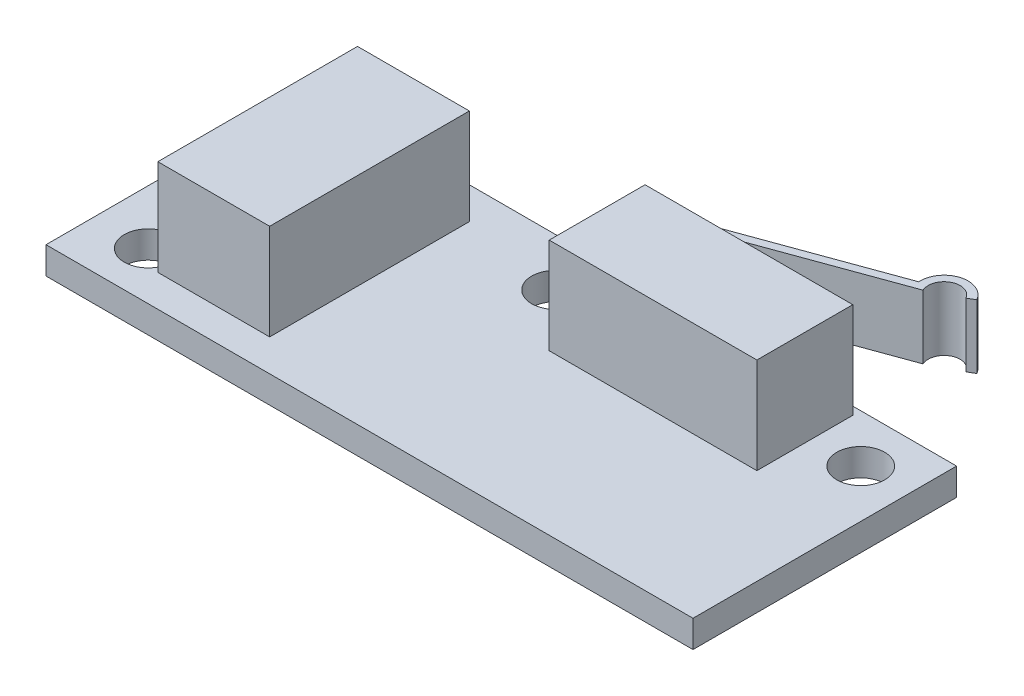
SolidWorks part; units mm, degrees
ref_plane "Front Plane" through (0, 0, 0) normal (0, 0, 1) x (1, 0, 0)
ref_plane "Top Plane" through (0, 0, 0) normal (0, 1, 0) x (1, 0, 0)
ref_plane "Right Plane" through (0, 0, 0) normal (1, 0, 0) x (0, 0, -1)
sketch "Sketch1" plane through (0, 0, 0) normal (0, 1, 0) x (1, 0, 0)
  line L1 (0, 0) -> (40.5, 0)
  line L2 (0, 0) -> (0, 16.5)
  line L3 (0, 16.5) -> (40.5, 16.5)
  line L4 (40.5, 0) -> (40.5, 16.5)
  circle A0 centre (3.4, 3) radius 1.5
  circle A1 centre (3.4, 13.5) radius 1.5
  circle A2 centre (18.4, 13.5) radius 1.5
  circle A3 centre (37.5, 13.5) radius 1.5
  dimension "D3" = 3
  dimension "D5" = 3
  dimension "D6" = 3
  dimension "D7" = 3
  dimension "D8" = 15
  dimension "D1" = 16.5
  dimension "D2" = 40.5
  dimension "D4" = 3.4
extrude "Boss-Extrude1" add sketch "Sketch1" along normal blind 1.7
sketch "Sketch2" plane through (0, 1.7, 0) normal (0, 1, 0) x (1, 0, 0)
  line L0 (0, 16.5) -> (0, 0) construction
  line L1 (5, 14.5) -> (12, 14.5)
  line L2 (5, 14.5) -> (5, 2)
  line L3 (5, 2) -> (12, 2)
  line L4 (12, 14.5) -> (12, 2)
  point P4 (5, 8.25)
  point P7 (0, 8.25)
  dimension "D1" = 7
  dimension "D2" = 12.5
  dimension "D3" = 5
extrude "Boss-Extrude2" add sketch "Sketch2" along normal blind 6 separate body
shell "Shell1" thickness 0.5
sketch "Sketch3" plane through (0, 1.7, 0) normal (0, 1, 0) x (1, 0, 0)
  line L0 (40.5, 0) -> (40.5, 16.5) construction
  line L2 (21.5, 16) -> (21.5, 10)
  line L3 (21.5, 10) -> (34.5, 10)
  line L4 (34.5, 16) -> (34.5, 10)
  line L5 (36.6872, 20.8977) -> (37.1202, 21.1477)
  line L6 (21.5, 16) -> (22.5, 16)
  line L7 (22.5, 16) -> (34.3242, 20.3036)
  line L8 (23.9619, 16) -> (34.5, 16)
  line L9 (23.9619, 16) -> (34.9104, 19.9849)
  line L10 (40.5, 16.5) -> (0, 16.5) construction
  line L11 (36.6872, 20.8977) -> (36.1282, 21.8659) construction
  arc A0 (34.3242, 20.3036) -> (37.1202, 21.1477) centre (35.8212, 20.3977) cw
  arc A1 (34.9104, 19.9849) -> (36.6872, 20.8977) centre (35.8212, 20.3977) cw
  dimension "D7" = 1.5
  dimension "D9" = 0.5
  dimension "D1" = 13
  dimension "D2" = 6
  dimension "D3" = 19
  dimension "D4" = 0.5
  dimension "D5" = 0.5
  dimension "D6" = 1
  dimension "D8" = 20
  dimension "D10" = 15.5
  dimension "D11" = 10
  dimension "D12" = 0.25
extrude "Boss-Extrude3" add sketch "Sketch3" along normal blind 6
sketch "Sketch4" plane through (0, 7.7, 0) normal (0, 1, 0) x (1, 0, 0)
  line L1 (22.5, 16) -> (37.1202, 16)
  line L2 (22.5, 16) -> (22.5, 21.8977)
  line L3 (22.5, 21.8977) -> (37.1202, 21.8977)
  line L4 (37.1202, 16) -> (37.1202, 21.8977)
  arc A0 (37.1202, 21.1477) -> (34.3242, 20.3036) centre (35.8212, 20.3977) ccw construction
extrude "Cut-Extrude1" cut sketch "Sketch4" against normal blind 1
sketch "Sketch5" plane through (0, 1.7, 0) normal (0, -1, 0) x (1, 0, 0)
  line L1 (23.8737, -16.5) -> (37.1202, -16.5)
  line L2 (23.8737, -16.5) -> (23.8737, -21.8977)
  line L3 (23.8737, -21.8977) -> (37.1202, -21.8977)
  line L4 (37.1202, -16.5) -> (37.1202, -21.8977)
  arc A0 (34.3242, -20.3036) -> (37.1202, -21.1477) centre (35.8212, -20.3977) ccw construction
extrude "Cut-Extrude2" cut sketch "Sketch5" against normal blind 1
